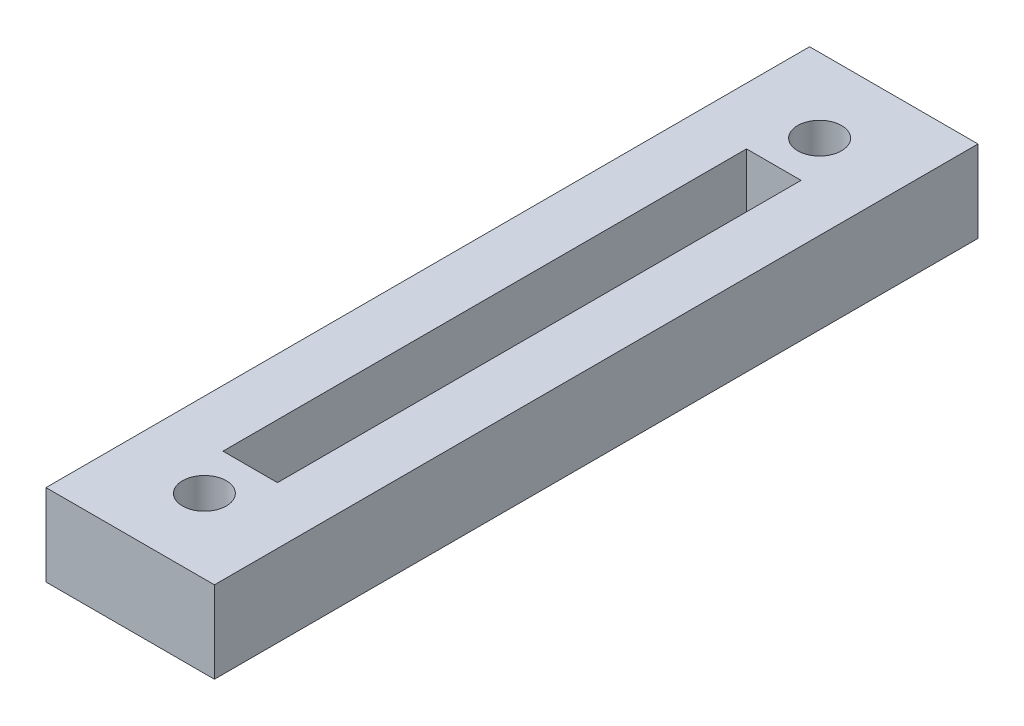
SolidWorks part; units mm, degrees
material "6061 Alloy"
ref_plane "Front Plane" through (0, 0, 0) normal (0, 0, 1) x (1, 0, 0)
ref_plane "Top Plane" through (0, 0, 0) normal (0, 1, 0) x (1, 0, 0)
ref_plane "Right Plane" through (0, 0, 0) normal (1, 0, 0) x (0, 0, -1)
sketch "Sketch1" plane through (0, 0, 0) normal (0, 1, 0) x (1, 0, 0)
  line L0 (9.8044, 88.9) -> (9.8044, 80.264) construction
  line L1 (0, 0) -> (19.6088, 0)
  line L2 (0, 0) -> (0, 88.9)
  line L3 (0, 88.9) -> (19.6088, 88.9)
  line L4 (19.6088, 0) -> (19.6088, 88.9)
  line L5 (9.8044, 80.264) -> (9.8044, 8.636) construction
  line L6 (9.8044, 8.636) -> (9.8044, 0) construction
  circle A0 centre (9.8044, 80.264) radius 2.54
  circle A1 centre (9.8044, 8.636) radius 2.54
  point P11 (9.8044, 44.45)
  dimension "D3" = 5.08
  dimension "D1" = 19.6088
  dimension "D2" = 88.9
  dimension "D4" = 71.628
extrude "Boss-Extrude1" add sketch "Sketch1" along normal blind 9.525
ref_plane "Plane1" through (0, 0, -44.45) normal (0, 0, 1) x (1, 0, 0)
sketch "Sketch2" plane through (0, 9.525, 0) normal (0, 1, 0) x (1, 0, 0)
  line L0 (9.8044, 88.9) -> (9.8044, 0) construction
  line L1 (19.6088, 88.9) -> (0, 88.9) construction
  line L2 (0, 0) -> (19.6088, 0) construction
  line L4 (6.6294, 74.93) -> (12.9794, 74.93)
  line L5 (6.6294, 74.93) -> (6.6294, 13.97)
  line L6 (6.6294, 13.97) -> (12.9794, 13.97)
  line L7 (12.9794, 74.93) -> (12.9794, 13.97)
  line L8 (6.6294, 74.93) -> (12.9794, 13.97) construction
  line L9 (6.6294, 13.97) -> (12.9794, 74.93) construction
  point P6 (9.8044, 44.45)
  dimension "D1" = 6.35
  dimension "D2" = 60.96
extrude "Cut-Extrude1" cut sketch "Sketch2" against normal blind 6.477
hole_wizard "#10-32 Tapped Hole4" positions "Sketch4" profile "Sketch3" tap size "1/4-20" standard "ANSI Inch"
sketch "Sketch4" plane through (0, 9.525, 0) normal (0, 1, 0) x (1, 0, 0)
  point P1 (9.8044, 80.264)
  point P4 (9.8044, 8.636)
sketch "Sketch3" plane through (9.8044, 9.525, -80.264) normal (1, 0, 0) x (0, 0, 1)
  line L0 (0, 0) -> (0, 18.0438)
  line L1 (0, 18.0438) -> (2.5527, 16.51)
  line L2 (2.5527, 16.51) -> (2.5527, 0)
  line L5 (2.5527, 0) -> (0, 0)
  line L10 (0, 18.0438) -> (-2.5527, 16.51) construction
  line L11 (0, -6.35) -> (0, 107.95) construction
  dimension "Tap Drill Dia." = 5.1054
  dimension "Tap Drill Depth" = 16.51
  dimension "Drill Angle" = 118
cosmetic thread "Hole Thread4" parameters "D1"=9.525, "D2"=6.35
cosmetic thread "Hole Thread5" parameters "D1"=9.525, "D2"=6.35
equation "\"base length\"= 21"
equation "\"glass pane length\"= 14.125"
equation "\"glass pane width\"= 10.1875"
equation "\"glass pane wall width\"= 3/4"
equation "\"glass lip\"= 1/4"
equation "\"bolt diameter\"= 0.2"
equation "\"stepper body width\"= 2.22"
equation "\"stepper mount offset\"= 0.19"
equation "\"stepper mount diameter\"= 0.19"
equation "\"stepper shaft offset from body\"= 0.79"
equation "\"stepper spacer thickness\"= 0.2"
equation "\"y axis stepper wall height off base\"= 8"
equation "\"y axis stepper wall bracket thickness\"= 1"
equation "\"y axis stepper wall mount side offset\"= 1/2"
equation "\"y axis stepper wall mount top offset\"= 1/2"
equation "\"y axis stepper wall width\"= \"stepper body width\" + 1                  "
equation "\"y axis bracket height to hole\"= 3.5"
equation "\"thin metal\"= 0.12"
equation "\"thick metal\"= 0.25"
equation "\"foot diameter\"= 0.2"
equation "\"foot inset from corner\"= 1"
equation "\"recognizer width\"= 2.5"
equation "\"recognizer nut plate height\"= 1.25"
equation "\"recognizer nut plate offset\"= 1.5"
equation "\"recognizer arm length\"= 7"
equation "\"recognizer bracket length\"= 4"
equation "\"D3@Sketch1\"=\"bolt diameter\""
